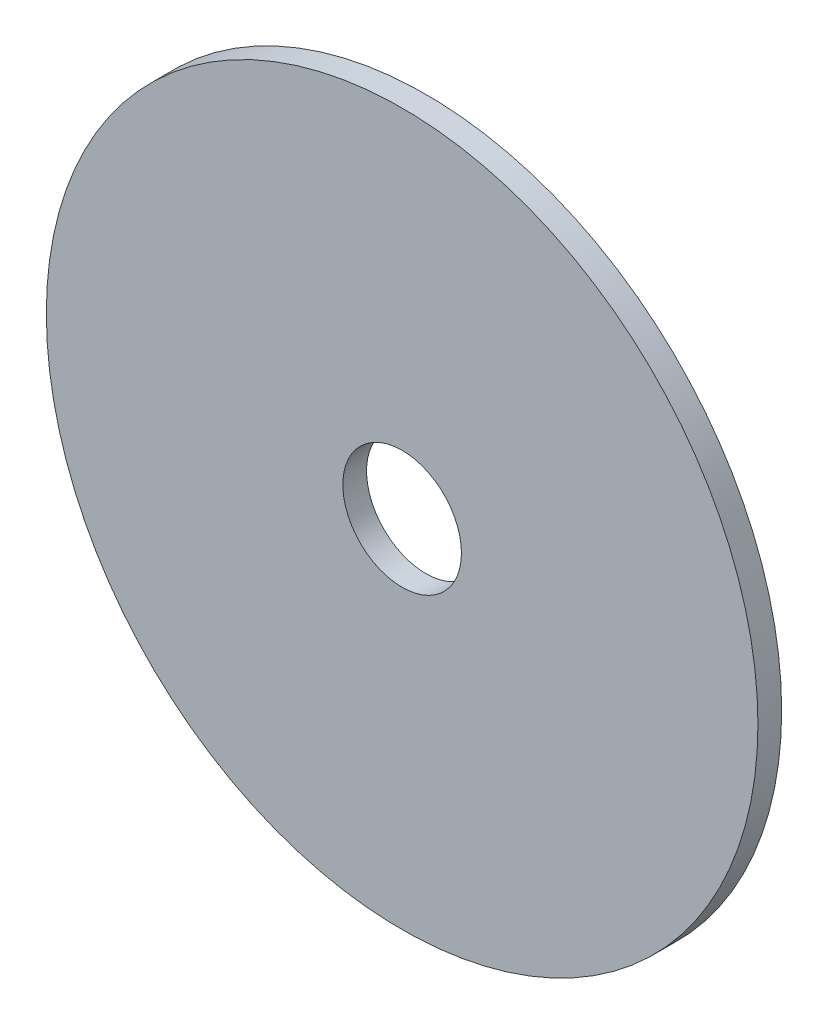
SolidWorks part; units mm, degrees
ref_plane "Front Plane" through (0, 0, 0) normal (0, 0, 1) x (1, 0, 0)
ref_plane "Top Plane" through (0, 0, 0) normal (0, 1, 0) x (1, 0, 0)
ref_plane "Right Plane" through (0, 0, 0) normal (1, 0, 0) x (0, 0, -1)
sketch "Sketch1" plane through (0, 0, 0) normal (0, 0, 1) x (1, 0, 0)
  circle A0 centre (0, 0) radius 30
extrude "Boss-Extrude1" add sketch "Sketch1" along normal blind 2
sketch "Sketch2" plane through (0, 0, 2) normal (0, 0, 1) x (1, 0, 0)
  circle A0 centre (0, 0) radius 5
extrude "Cut-Extrude1" cut sketch "Sketch2" against normal blind 4
